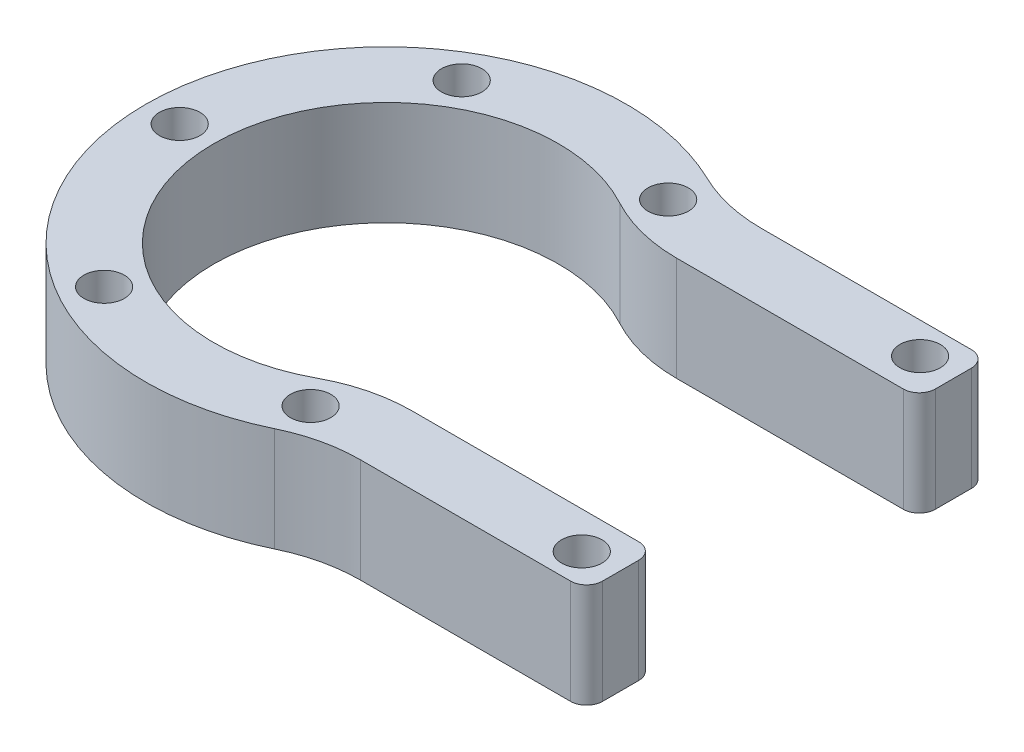
SolidWorks part; units mm, degrees
material "ABS"
ref_plane "前视基准面" through (0, 0, 0) normal (0, 0, 1) x (1, 0, 0)
ref_plane "上视基准面" through (0, 0, 0) normal (0, 1, 0) x (1, 0, 0)
ref_plane "右视基准面" through (0, 0, 0) normal (1, 0, 0) x (0, 0, -1)
other "Configuration Table"
sketch "草图1" plane through (0, 0, 0) normal (0, 1, 0) x (1, 0, 0)
  line L1 (16.5831, -25) -> (70, -25)
  line L2 (16.5831, -25) -> (16.5831, 25)
  line L3 (16.5831, 25) -> (70, 25)
  line L4 (70, -25) -> (70, 25)
  line L5 (16.5831, -25) -> (70, 25) construction
  line L6 (16.5831, 25) -> (70, -25) construction
  circle A0 centre (0, 0) radius 30
  point P3 (43.2916, 0)
  dimension "D1" = 60
  dimension "D2" = 70
  dimension "D3" = 50
extrude "凸台-拉伸1" add sketch "草图1" along normal blind 13 contours L2 A0 | L2 A0 | A0 L1 L4 L3
sketch "草图2" plane through (0, 13, 0) normal (0, 1, 0) x (1, 0, 0)
  circle A0 centre (0, 0) radius 25.75 construction
  circle A1 centre (-25.75, 0) radius 2.525
  circle A2 centre (-12.875, 22.3002) radius 2.525
  circle A3 centre (12.875, 22.3002) radius 2.525
  circle A4 centre (25.75, 0) radius 2.525
  circle A5 centre (12.875, -22.3002) radius 2.525
  circle A6 centre (-12.875, -22.3002) radius 2.525
  point P21 (0, 0)
  dimension "D1" = 51.5
  dimension "D2" = 5.05
  dimension "D3" = 6
extrude "切除-拉伸1" cut sketch "草图2" against normal through all
sketch "草图3" plane through (0, 13, 0) normal (0, 1, 0) x (1, 0, 0)
  line L6 (70, -16.5) -> (13.784, -16.5)
  line L7 (13.784, 16.5) -> (70, 16.5)
  line L8 (70, -16.5) -> (13.784, -16.5)
  line L9 (13.784, 16.5) -> (70, 16.5)
  line L10 (52, -25) -> (52, 25)
  line L11 (52, -25) -> (52, 25)
  arc A3 (13.784, 16.5) -> (13.784, -16.5) centre (0, 0) ccw
  arc A4 (13.784, 16.5) -> (13.784, -16.5) centre (0, 0) ccw
  circle M9 centre (12.875, -22.3002) radius 2.525
  dimension "D1" = 8.5
  dimension "D2" = 18
extrude "切除-拉伸2" cut sketch "草图3" against normal through all contours L9 A4 L8 L11 M9
sketch "草图4" plane through (0, 13, 0) normal (0, 1, 0) x (1, 0, 0)
  line L0 (0, 0) -> (50000, 0) construction
  circle A0 centre (45.5, 21.1) radius 2.525
  circle A1 centre (45.5, -21.1) radius 2.525
  dimension "D3" = 5.05
  dimension "D1" = 45.5
  dimension "D2" = 21.1
extrude "切除-拉伸3" cut sketch "草图4" against normal through all
sketch "草图5" plane through (0, 13, 0) normal (0, 1, 0) x (1, 0, 0)
  line L0 (16.5831, -25) -> (70, -25) construction
  line L1 (70, 25) -> (62, 25)
  line L2 (70, 25) -> (70, -25)
  line L3 (70, -25) -> (62, -25)
  line L4 (62, 25) -> (62, -25)
  dimension "D1" = 62
extrude "切除-拉伸4" cut sketch "草图5" against normal through all contours L2 L1 L4 L3
sketch "草图6" plane through (0, 13, 0) normal (0, 1, 0) x (1, 0, 0)
  line L0 (56, 5.9314) -> (56, 50005.9314) construction
  line L1 (56, 0) -> (50056, 0) construction
  circle A0 centre (56, 0) radius 1.525
  circle A1 centre (56, 15) radius 1.525
  circle A2 centre (56, -15) radius 1.525
  dimension "D2" = 3.05
  dimension "D1" = 56
  dimension "D3" = 15
extrude "切除-拉伸5" cut sketch "草图6" against normal through all
sketch "草图7" plane through (0, 13, 0) normal (0, 1, 0) x (1, 0, 0)
  line L0 (16.5831, 25) -> (62, 25) construction
  line L1 (50, 25) -> (62, 25)
  line L2 (50, 25) -> (50, -30)
  line L3 (50, -30) -> (62, -30)
  line L4 (62, 25) -> (62, -30)
  line L5 (62, 25) -> (62, -25) construction
  dimension "D1" = 55
  dimension "D2" = 12
extrude "切除-拉伸6" cut sketch "草图7" against normal through all
fillet "圆角1" radius 20 2 edges at (13.784, 6.5, 16.5) (13.784, 6.5, -16.5)
fillet "圆角2" radius 20 2 edges at (16.5831, 6.5, -25) (16.5831, 6.5, 25)
fillet "圆角3" radius 2 4 edges at (50, 6.5, -16.5) (50, 6.5, -25) (50, 6.5, 16.5) (50, 6.5, 25)
sketch "草图9" plane through (0, 0, 0) normal (1, 0, 0) x (0, 0, -1)
  text T0 "热" font "汉仪长仿宋体" height in points 22
  text T2 "我" font "汉仪长仿宋体" height in points 22
  text T5 "爱" font "汉仪长仿宋体" height in points 22
  point P6 (0, 0)
